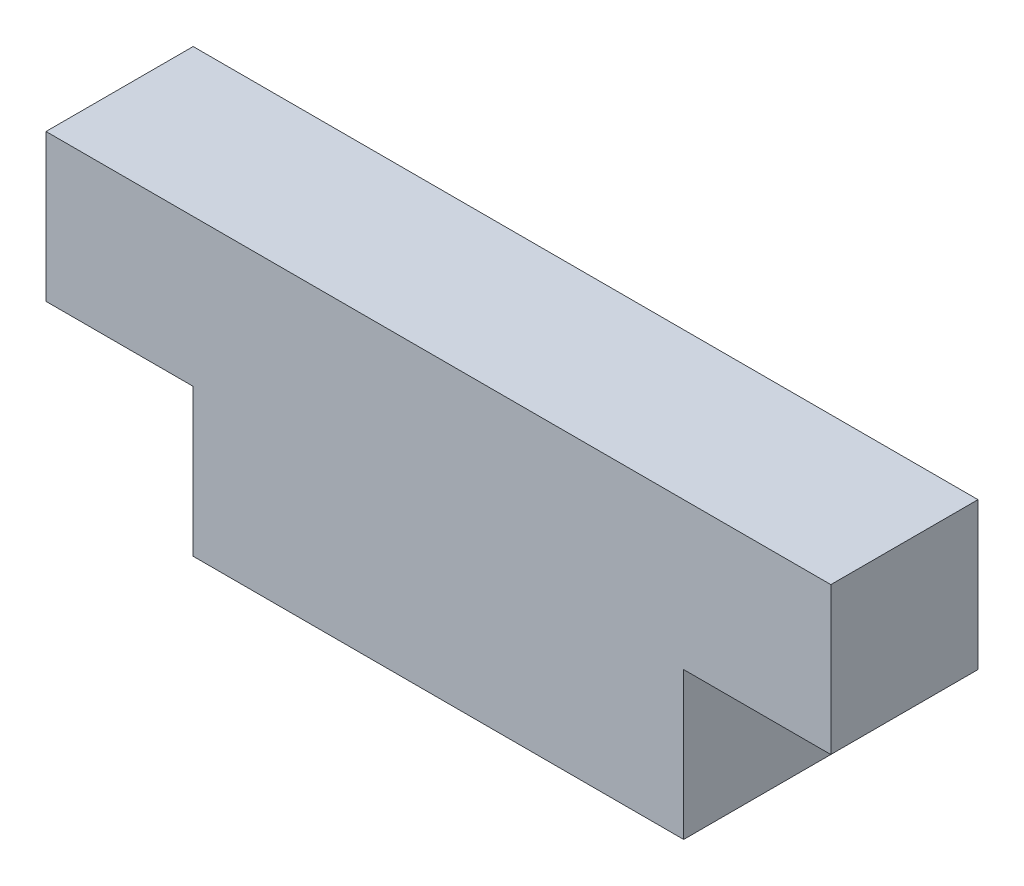
SolidWorks part; units mm, degrees
ref_plane "Alzado" through (0, 0, 0) normal (0, 0, 1) x (1, 0, 0)
ref_plane "Planta" through (0, 0, 0) normal (0, 1, 0) x (1, 0, 0)
ref_plane "Vista lateral" through (0, 0, 0) normal (1, 0, 0) x (0, 0, -1)
sketch "Croquis1" plane through (0, 0, 0) normal (0, 1, 0) x (1, 0, 0)
  line L1 (5, -1.5) -> (-5, -1.5)
  line L2 (5, -1.5) -> (5, 1.5)
  line L3 (5, 1.5) -> (-5, 1.5)
  line L4 (-5, -1.5) -> (-5, 1.5)
  line L5 (5, -1.5) -> (-5, 1.5) construction
  line L6 (5, 1.5) -> (-5, -1.5) construction
  point P0 (0, 0)
  dimension "D1" = 10
  dimension "D2" = 3
extrude "Saliente-Extruir1" add sketch "Croquis1" along normal blind 3
sketch "Croquis2" plane through (0, 3, 0) normal (0, 1, 0) x (1, 0, 0)
  line L1 (8, -1.5) -> (-8, -1.5)
  line L2 (8, -1.5) -> (8, 1.5)
  line L3 (8, 1.5) -> (-8, 1.5)
  line L4 (-8, -1.5) -> (-8, 1.5)
  line L5 (8, -1.5) -> (-8, 1.5) construction
  line L6 (8, 1.5) -> (-8, -1.5) construction
  point P0 (0, 0)
  dimension "D1" = 3
  dimension "D2" = 16
extrude "Saliente-Extruir2" add sketch "Croquis2" along normal blind 3
